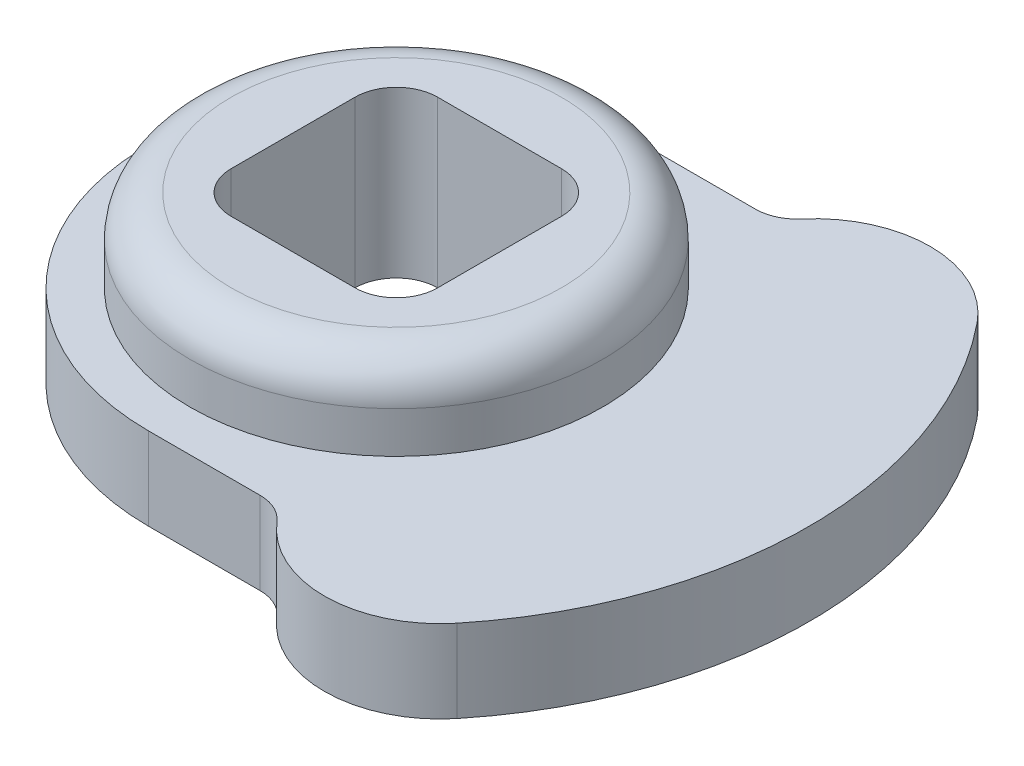
SolidWorks part; units mm, degrees
material "Plain Carbon Steel"
ref_plane "Front Plane" through (0, 0, 0) normal (0, 0, 1) x (1, 0, 0)
ref_plane "Top Plane" through (0, 0, 0) normal (0, 1, 0) x (1, 0, 0)
ref_plane "Right Plane" through (0, 0, 0) normal (1, 0, 0) x (0, 0, -1)
sketch "Sketch1" plane through (0, 0, 0) normal (0, 1, 0) x (1, 0, 0)
  circle A0 centre (0, 0) radius 6.35
  dimension "D1" = 12.7
extrude "Boss-Extrude1" add sketch "Sketch1" along normal blind 5.08
sketch "Sketch3" plane through (0, 0, 0) normal (0, 1, 0) x (1, 0, 0)
  line L0 (0, 0) -> (14.4417, 0) construction
  line L1 (0, 7.62) -> (3.429, 7.62)
  line L2 (0, -7.62) -> (3.429, -7.62)
  arc A1 (3.429, 7.62) -> (4.3956, 8.0662) centre (3.429, 8.89) ccw
  circle A2 centre (0, 0) radius 7.62
  arc A3 (0, 7.62) -> (0, -7.62) centre (0, 0) ccw
  arc A4 (4.3956, 8.0662) -> (9.864, 7.9995) centre (7.102, 5.7597) cw
  arc A5 (4.3956, -8.0662) -> (9.864, -7.9995) centre (7.102, -5.7597) ccw
  arc A6 (3.429, -7.62) -> (4.3956, -8.0662) centre (3.429, -8.89) cw
  arc A7 (9.864, 7.9995) -> (9.864, -7.9995) centre (0, 0) cw
  dimension "D2" = 12.7
  dimension "D3" = 1.27
  dimension "D4" = 3.556
  dimension "D5" = 3.429
  dimension "D1" = 1.27
extrude "Boss-Extrude2" add sketch "Sketch3" along normal blind 2.54
sketch "Sketch4" plane through (0, 5.08, 0) normal (0, 1, 0) x (1, 0, 0)
  line L1 (-1.905, 3.175) -> (1.905, 3.175)
  line L2 (-3.175, 1.905) -> (-3.175, -1.905)
  line L3 (-1.905, -3.175) -> (1.905, -3.175)
  line L4 (3.175, 1.905) -> (3.175, -1.905)
  line L5 (-3.175, 3.175) -> (3.175, -3.175) construction
  line L6 (-3.175, -3.175) -> (3.175, 3.175) construction
  arc A0 (-3.175, -1.905) -> (-1.905, -3.175) centre (-1.905, -1.905) ccw
  arc A1 (1.905, -3.175) -> (3.175, -1.905) centre (1.905, -1.905) ccw
  arc A2 (3.175, 1.905) -> (1.905, 3.175) centre (1.905, 1.905) ccw
  arc A3 (-1.905, 3.175) -> (-3.175, 1.905) centre (-1.905, 1.905) ccw
  point P0 (0, 0)
  dimension "D3" = 1.27
  dimension "D1" = 6.35
  dimension "D2" = 6.35
extrude "Cut-Extrude1" cut sketch "Sketch4" against normal through all
fillet "Fillet1" radius 1.27 1 edges at (0, 5.08, 6.35)
